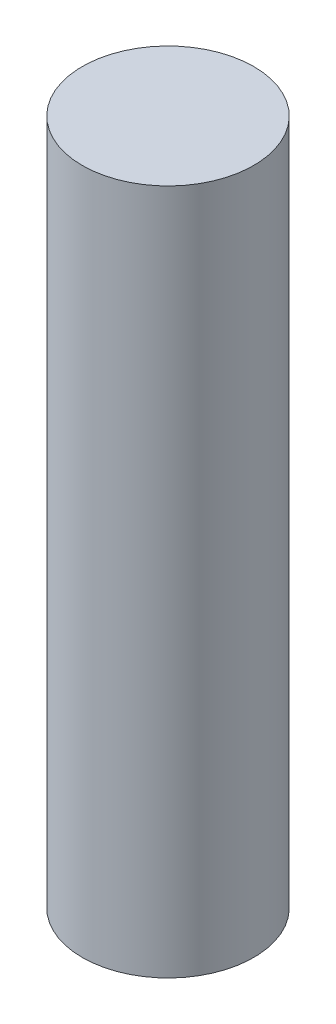
SolidWorks part; units mm, degrees
ref_plane "Front" through (0, 0, 0) normal (0, 0, 1) x (1, 0, 0)
ref_plane "Top" through (0, 0, 0) normal (0, 1, 0) x (1, 0, 0)
ref_plane "Right" through (0, 0, 0) normal (1, 0, 0) x (0, 0, -1)
sketch "Sketch1" plane through (0, 0, 0) normal (0, 1, 0) x (1, 0, 0)
  circle A0 centre (0, 0) radius 3.175
  dimension "D1" = 6.35
extrude "Boss-Extrude1" add sketch "Sketch1" along normal blind 25.4
